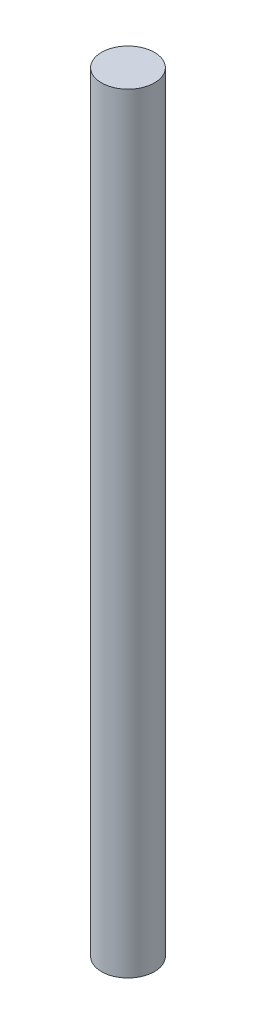
SolidWorks part; units mm, degrees
ref_plane "Front Plane" through (0, 0, 0) normal (0, 0, 1) x (1, 0, 0)
ref_plane "Top Plane" through (0, 0, 0) normal (0, 1, 0) x (1, 0, 0)
ref_plane "Right Plane" through (0, 0, 0) normal (1, 0, 0) x (0, 0, -1)
sketch "Sketch1" plane through (0, 0, 0) normal (0, 1, 0) x (1, 0, 0)
  circle A0 centre (0, 0) radius 11
  dimension "D1" = 22
extrude "Boss-Extrude1" add sketch "Sketch1" along normal blind 320
